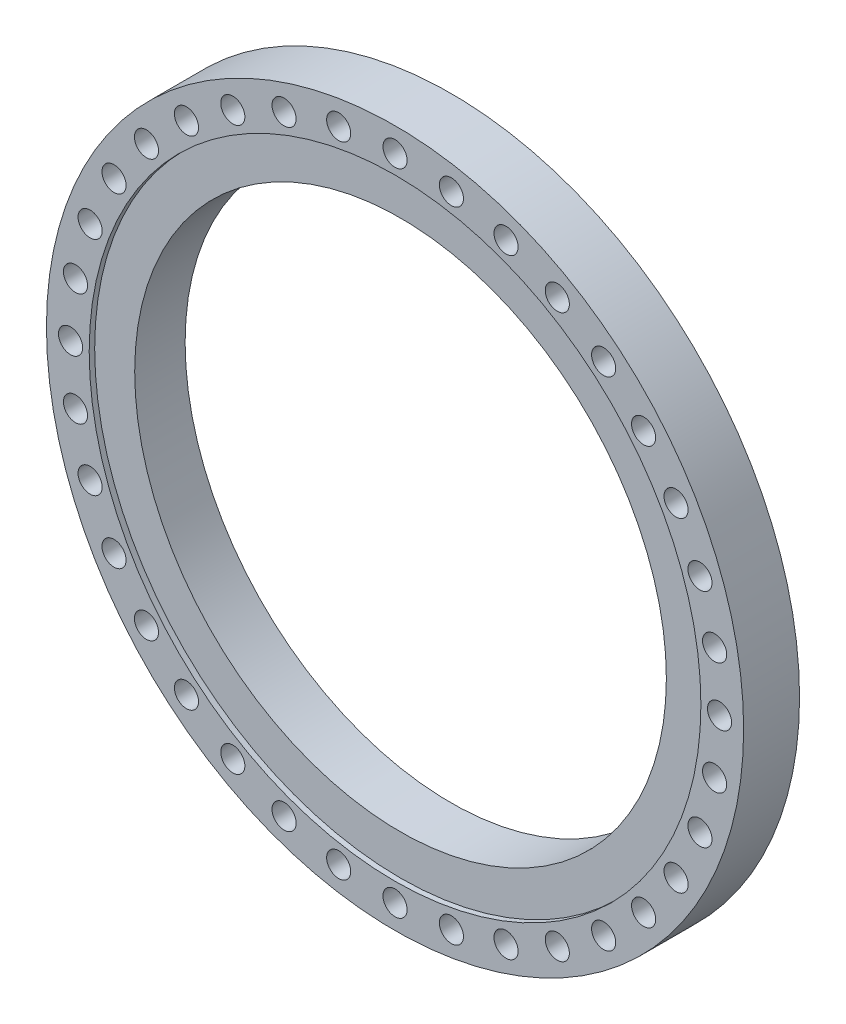
SolidWorks part; units mm, degrees
material "AISI 304"
ref_plane "Front Plane" through (0, 0, 0) normal (0, 0, 1) x (1, 0, 0)
ref_plane "Top Plane" through (0, 0, 0) normal (0, 1, 0) x (1, 0, 0)
ref_plane "Right Plane" through (0, 0, 0) normal (1, 0, 0) x (0, 0, -1)
sketch "Sketch1" plane through (0, 0, 0) normal (0, 0, 1) x (1, 0, 0)
  circle A0 centre (0, 0) radius 318
  circle A1 centre (0, 0) radius 242.5
  dimension "D1" = 636
  dimension "D2" = 485
extrude "Boss-Extrude1" add sketch "Sketch1" along normal mid plane 51
sketch "Sketch2" plane through (0, 0, 25.5) normal (0, 0, 1) x (1, 0, 0)
  circle A0 centre (0, 0) radius 279
  dimension "D1" = 558
extrude "Cut-Extrude1" cut sketch "Sketch2" against normal blind 5
sketch "Sketch3" plane through (0, 0, 0) normal (0, 0, 1) x (1, 0, 0)
  circle A0 centre (0, 0) radius 296 construction
  circle A1 centre (0, 296) radius 11
  circle A2 centre (51.3999, 291.5031) radius 11
  circle A3 centre (101.238, 278.149) radius 11
  circle A4 centre (148, 256.3435) radius 11
  circle A5 centre (190.2651, 226.7492) radius 11
  circle A6 centre (226.7492, 190.2651) radius 11
  circle A7 centre (256.3435, 148) radius 11
  circle A8 centre (278.149, 101.238) radius 11
  circle A9 centre (291.5031, 51.3999) radius 11
  circle A10 centre (296, 0) radius 11
  circle A11 centre (291.5031, -51.3999) radius 11
  circle A12 centre (278.149, -101.238) radius 11
  circle A13 centre (256.3435, -148) radius 11
  circle A14 centre (226.7492, -190.2651) radius 11
  circle A15 centre (190.2651, -226.7492) radius 11
  circle A16 centre (148, -256.3435) radius 11
  circle A17 centre (101.238, -278.149) radius 11
  circle A18 centre (51.3999, -291.5031) radius 11
  circle A19 centre (0, -296) radius 11
  circle A20 centre (-51.3999, -291.5031) radius 11
  circle A21 centre (-101.238, -278.149) radius 11
  circle A22 centre (-148, -256.3435) radius 11
  circle A23 centre (-190.2651, -226.7492) radius 11
  circle A24 centre (-226.7492, -190.2651) radius 11
  circle A25 centre (-256.3435, -148) radius 11
  circle A26 centre (-278.149, -101.238) radius 11
  circle A27 centre (-291.5031, -51.3999) radius 11
  circle A28 centre (-296, 0) radius 11
  circle A29 centre (-291.5031, 51.3999) radius 11
  circle A30 centre (-278.149, 101.238) radius 11
  circle A31 centre (-256.3435, 148) radius 11
  circle A32 centre (-226.7492, 190.2651) radius 11
  circle A33 centre (-190.2651, 226.7492) radius 11
  circle A34 centre (-148, 256.3435) radius 11
  circle A35 centre (-101.238, 278.149) radius 11
  circle A36 centre (-51.3999, 291.5031) radius 11
  dimension "D1" = 592
  dimension "D2" = 22
  dimension "D3" = 36
extrude "Cut-Extrude2" cut sketch "Sketch3" against normal mid plane 55
